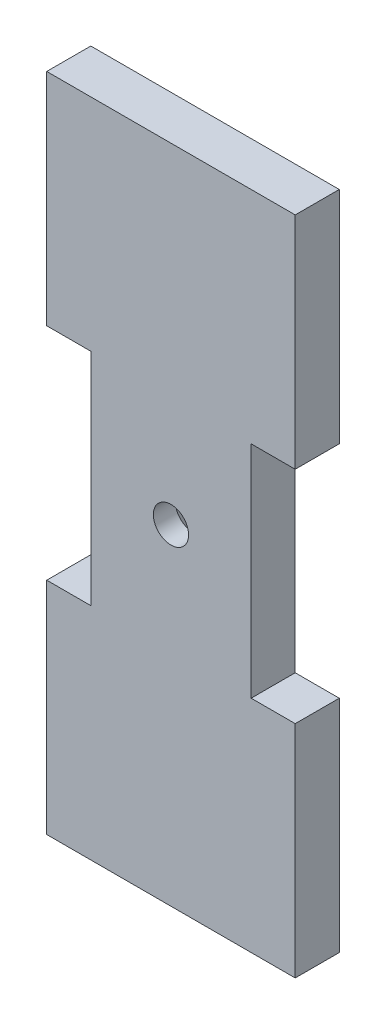
SolidWorks part; units mm, degrees
ref_plane "Front Plane" through (0, 0, 0) normal (0, 0, 1) x (1, 0, 0)
ref_plane "Top Plane" through (0, 0, 0) normal (0, 1, 0) x (1, 0, 0)
ref_plane "Right Plane" through (0, 0, 0) normal (1, 0, 0) x (0, 0, -1)
sketch "Sketch1" plane through (0, 0, 0) normal (0, 0, 1) x (1, 0, 0)
  line L0 (0, 150) -> (56.4, 150)
  line L1 (0, 0) -> (56.4, 0) construction
  line L2 (0, 0) -> (0, 150) construction
  line L3 (0, 150) -> (56.4, 150) construction
  line L4 (56.4, 0) -> (56.4, 150) construction
  line L5 (56.4, 150) -> (56.4, 100)
  line L6 (56.4, 100) -> (46.4, 100)
  line L7 (46.4, 100) -> (46.4, 50)
  line L8 (46.4, 50) -> (56.4, 50)
  line L9 (56.4, 50) -> (56.4, 0)
  line L10 (56.4, 0) -> (0, 0)
  line L11 (28.2, 150) -> (28.2, 0) construction
  line L12 (0, 150) -> (0, 100)
  line L13 (0, 50) -> (0, 0)
  line L14 (10, 50) -> (0, 50)
  line L15 (10, 100) -> (10, 50)
  line L16 (0, 100) -> (10, 100)
  circle A0 centre (28.2, 75) radius 4
  dimension "D6" = 8
  dimension "D1" = 56.4
  dimension "D2" = 150
  dimension "D3" = 50
  dimension "D4" = 50
  dimension "D5" = 10
extrude "Boss-Extrude1" add sketch "Sketch1" along normal blind 10
chamfer "Chamfer1" distance 5 angle 45 1 edges at (32.2, 75, 0)
